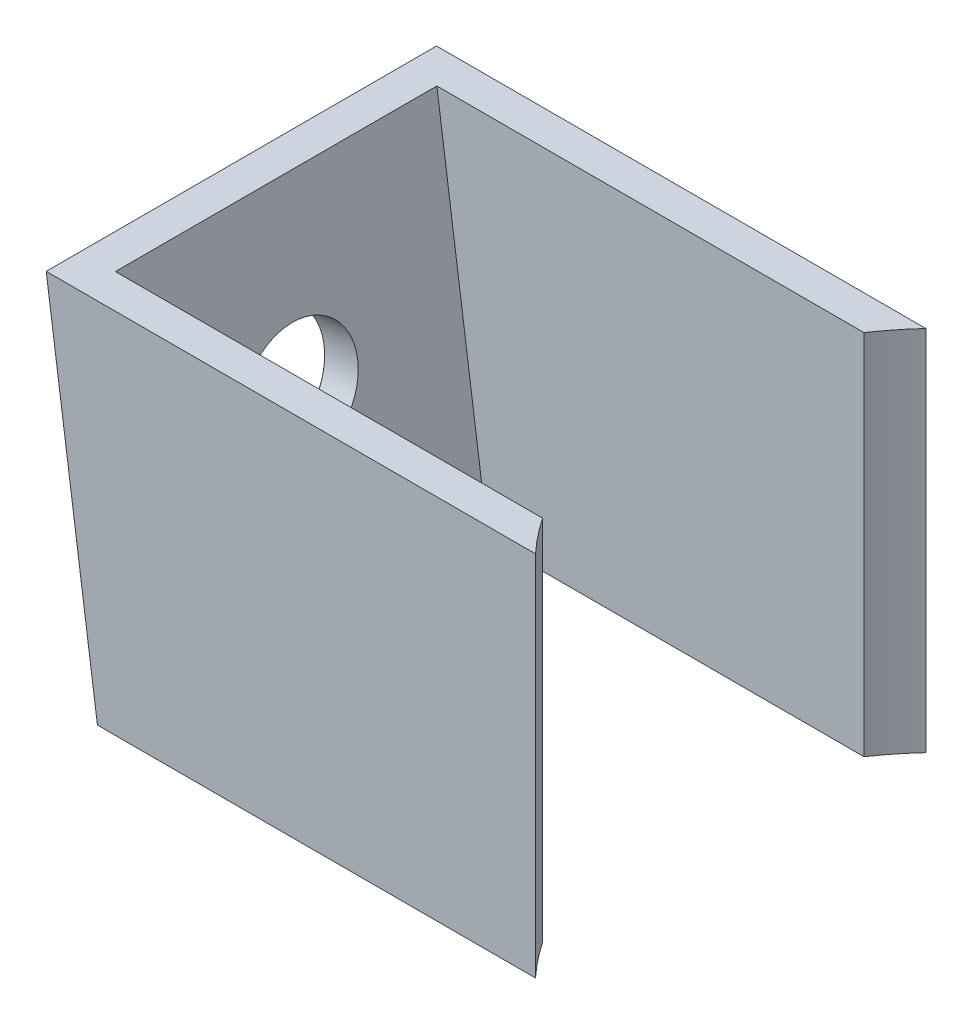
SolidWorks part; units mm, degrees
material "1.0545 (S355N)"
ref_plane "Płaszczyzna XY" through (0, 0, 0) normal (0, 0, 1) x (1, 0, 0)
ref_plane "Płaszczyzna XZ" through (0, 0, 0) normal (0, 1, 0) x (1, 0, 0)
ref_plane "Płaszczyzna YZ" through (0, 0, 0) normal (1, 0, 0) x (0, 0, -1)
sketch "Szkic1" plane through (0, 0, 0) normal (0, 0, 1) x (1, 0, 0)
  line L0 (-12.5, 0) -> (-87.4268, 0) construction
  line L1 (-9.6047, 8) -> (-30.9147, 8)
  line L2 (-30.9147, 8) -> (-28.6847, -8)
  line L3 (-9.6047, -8) -> (-28.6847, -8)
  line L4 (-9.6047, 8) -> (-9.6047, -8)
  dimension "D1" = 9.6047
  dimension "D2" = 8
  dimension "D3" = 21.31
  dimension "D4" = 8
  dimension "D5" = 19.08
extrude "Dodanie-wyciągnięcie1" add sketch "Szkic1" along normal blind 17
shell "Skorupa2" thickness 1.5
hole_wizard "Pogłębienie walcowe pod M2 Śrubę z łbem stożkowym ściętym1" positions "Szkic2" profile "Szkic3" counterbore size "M2" standard "ISO"
sketch "Szkic2" plane through (-29.2318, -4.0742, 0) normal (-0.9904, -0.138, 0) x (0, 0, 1)
  point P0 (8.5, 4.3666)
sketch "Szkic3" plane through (-29.8346, 0.2506, 8.5) normal (0, 0, 1) x (0.138, -0.9904, 0)
  line L0 (0, 0) -> (0, 10.721)
  line L1 (0, 10.721) -> (1.2, 10)
  line L2 (1.2, 10) -> (1.2, 1.6)
  line L3 (1.2, 1.6) -> (2.5, 1.6)
  line L5 (2.5, 1.6) -> (2.5, 0.025)
  line L6 (2.5, 0.025) -> (2.525, 0)
  line L7 (2.525, 0) -> (0, 0)
  line L8 (-2.5, 0.025) -> (-2.525, 0) construction
  line L10 (0, 10.721) -> (-1.2, 10) construction
  line L11 (0, -6.35) -> (0, 107.95) construction
  dimension "Średnica otworu" = 2.4
  dimension "Głębokość otworu" = 10
  dimension "Średnica pogłębienia walcowego" = 5
  dimension "Głębokość pogłębienia walcowego" = 1.6
  dimension "Średnica zewnętrznego pogłębienia stożkowego" = 5.05
  dimension "Kąt zewnętrznego pogłębienia stożkowego" = 90
  dimension "Kąt wiertła" = 118
sketch "Szkic5" plane through (0, 8, 0) normal (0, 1, 0) x (1, 0, 0)
  circle A0 centre (-0.4395, -8.5) radius 12.5
  dimension "D1" = 25
extrude "Wytnij-wyciągnięcie1" cut sketch "Szkic5" against normal blind 17
